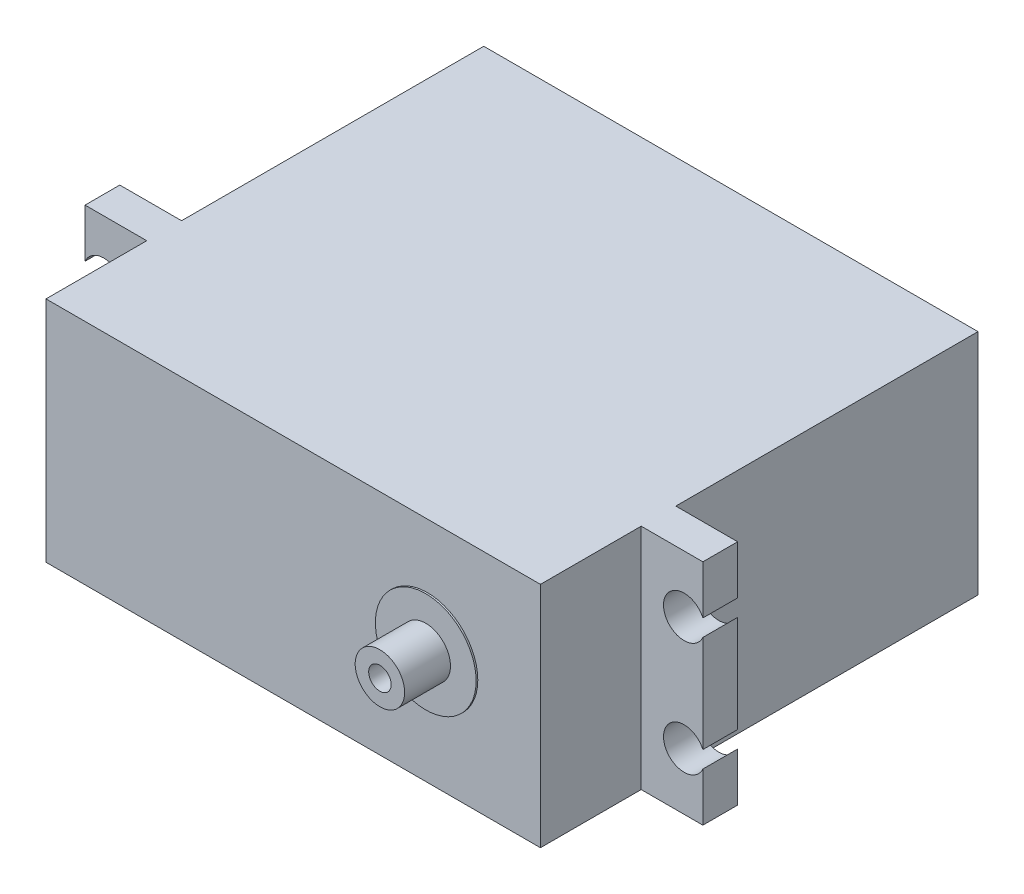
SolidWorks part; units mm, degrees
ref_plane "정면" through (0, 0, 0) normal (0, 0, 1) x (1, 0, 0)
ref_plane "윗면" through (0, 0, 0) normal (0, 1, 0) x (1, 0, 0)
ref_plane "우측면" through (0, 0, 0) normal (1, 0, 0) x (0, 0, -1)
sketch "스케치1" plane through (0, 0, 0) normal (0, 0, 1) x (1, 0, 0)
  line L1 (33.02, -15.24) -> (-33.02, -15.24)
  line L2 (33.02, -15.24) -> (33.02, 15.24)
  line L3 (33.02, 15.24) -> (-33.02, 15.24)
  line L4 (-33.02, -15.24) -> (-33.02, 15.24)
  line L5 (33.02, -15.24) -> (-33.02, 15.24) construction
  line L6 (33.02, 15.24) -> (-33.02, -15.24) construction
  point P0 (0, 0)
  dimension "D1" = 66.04
  dimension "D2" = 30.48
extrude "보스-돌출1" add sketch "스케치1" along normal blind 40.3754
ref_plane "평면1" through (0, 0, 40.3754) normal (0, 0, 1) x (1, 0, 0)
sketch "스케치2" plane through (0, 0, 40.3754) normal (0, 0, 1) x (1, 0, 0)
  line L0 (0, 15.24) -> (0, -15.24) construction
  line L1 (41.275, -15.24) -> (-41.275, -15.24)
  line L2 (-41.275, 8.7417) -> (-41.275, 15.24)
  line L3 (-41.275, -8.7417) -> (-41.275, -15.24)
  line L4 (-41.275, 8.7417) -> (-41.275, 15.24)
  line L5 (-41.275, -8.7417) -> (-41.275, -15.24)
  line L6 (-41.275, -8.7417) -> (-41.275, -15.24)
  line L7 (41.275, 15.24) -> (-41.275, 15.24)
  line L8 (41.275, -15.24) -> (-41.275, -15.24)
  line L9 (-41.275, 8.7417) -> (-41.275, 15.24)
  line L10 (-41.275, 6.4896) -> (-41.275, -6.4896)
  line L11 (-41.275, 0) -> (41.275, 0) construction
  line L12 (41.275, -15.24) -> (-41.275, -15.24)
  line L13 (-41.275, -8.7417) -> (-41.275, -15.24)
  line L14 (-41.275, 8.7417) -> (-41.275, 15.24)
  line L15 (41.275, 8.7417) -> (41.275, 15.24)
  line L16 (41.275, -8.7417) -> (41.275, -15.24)
  line L17 (41.275, 6.4896) -> (41.275, -6.4896)
  line L18 (41.275, 8.7417) -> (41.275, 15.24)
  line L19 (41.275, -8.7417) -> (41.275, -15.24)
  line L20 (41.275, -8.7417) -> (41.275, -15.24)
  line L21 (41.275, 8.7417) -> (41.275, 15.24)
  line L22 (41.275, -8.7417) -> (41.275, -15.24)
  line L23 (41.275, 8.7417) -> (41.275, 15.24)
  line L24 (-33.02, -15.24) -> (33.02, -15.24) construction
  line L25 (33.02, 15.24) -> (-33.02, 15.24) construction
  arc A0 (-41.275, -8.7417) -> (-41.275, -6.4896) centre (-38.7661, -7.6156) ccw
  arc A1 (-41.275, -8.7417) -> (-41.275, -6.4896) centre (-38.7661, -7.6156) ccw
  arc A2 (-41.275, 8.7417) -> (-41.275, 6.4896) centre (-38.7661, 7.6156) cw
  arc A3 (41.275, 8.7417) -> (41.275, 6.4896) centre (38.7661, 7.6156) ccw
  arc A4 (-41.275, 8.7417) -> (-41.275, 6.4896) centre (-38.7661, 7.6156) cw
  arc A5 (41.275, 8.7417) -> (41.275, 6.4896) centre (38.7661, 7.6156) ccw
  arc A6 (41.275, -8.7417) -> (41.275, -6.4896) centre (38.7661, -7.6156) cw
  arc A7 (41.275, -8.7417) -> (41.275, -6.4896) centre (38.7661, -7.6156) cw
  point P0 (-0.2214, 0.7433)
  point P3 (0, 0)
  dimension "D7" = 6.4983
  dimension "D8" = 12.9791
  dimension "D9" = 6.4983
  dimension "D5" = 2.75
  dimension "D6" = 2.75
  dimension "D1" = 82.55
  dimension "D2" = 6.4983
  dimension "D3" = 12.9791
  dimension "D4" = 6.4983
  dimension "D10" = 82.55
extrude "보스-돌출11" add sketch "스케치2" along normal blind 4.64 contours L16 A6 L17 A3 L15 L7 L2 A2 L10 A0 L3 L1
ref_plane "평면2" through (0, 0, 45.0154) normal (0, 0, 1) x (1, 0, 0)
sketch "스케치3" plane through (0, 0, 45.0154) normal (0, 0, 1) x (1, 0, 0)
  line L0 (41.275, 15.24) -> (-41.275, 15.24) construction
  line L1 (33.0324, -15.24) -> (-33.0324, -15.24)
  line L2 (33.0324, -15.24) -> (33.0324, 15.24)
  line L3 (33.0324, 15.24) -> (-33.0324, 15.24)
  line L4 (-33.0324, -15.24) -> (-33.0324, 15.24)
  line L5 (33.0324, -15.24) -> (-33.0324, 15.24) construction
  line L6 (33.0324, 15.24) -> (-33.0324, -15.24) construction
  point P0 (0, 0)
  dimension "D1" = 30.48
  dimension "D2" = 66.0647
extrude "보스-돌출12" add sketch "스케치3" along normal blind 13.462
ref_plane "평면3" through (0, 0, 58.4774) normal (0, 0, 1) x (1, 0, 0)
sketch "스케치5" plane through (0, 0, 58.4774) normal (0, 0, 1) x (1, 0, 0)
  line L0 (33.0324, -15.24) -> (33.0324, 15.24) construction
  circle A0 centre (17.9325, 0) radius 6.731
  circle A1 centre (17.9325, 0) radius 3.302
  dimension "D1" = 13.462
  dimension "D2" = 6.604
  dimension "D3" = 15.0999
extrude "보스-돌출13" add sketch "스케치5" along normal blind 0.2254
ref_plane "평면4" through (0, 0, 58.4774) normal (0, 0, 1) x (1, 0, 0)
sketch "스케치6" plane through (0, 0, 58.4774) normal (0, 0, 1) x (1, 0, 0)
  circle A0 centre (17.9325, 0) radius 3.302
  circle A1 centre (17.9325, 0) radius 1.5
  dimension "D1" = 6.604
  dimension "D2" = 3
extrude "보스-돌출14" add sketch "스케치6" along normal blind 6.35
